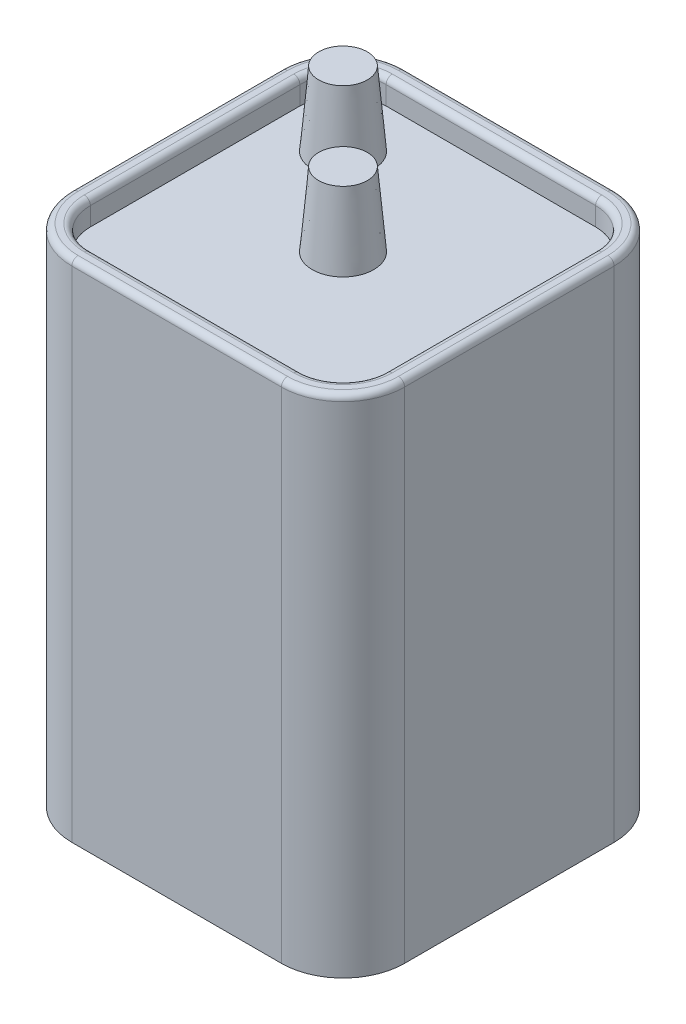
SolidWorks part; units mm, degrees
ref_plane "Front Plane" through (0, 0, 0) normal (0, 0, 1) x (1, 0, 0)
ref_plane "Top Plane" through (0, 0, 0) normal (0, 1, 0) x (1, 0, 0)
ref_plane "Right Plane" through (0, 0, 0) normal (1, 0, 0) x (0, 0, -1)
sketch "Sketch2" plane through (0, 0, 0) normal (0, 1, 0) x (1, 0, 0)
  line L1 (-34.29, 34.29) -> (34.29, 34.29)
  line L2 (-34.29, 34.29) -> (-34.29, -34.29)
  line L3 (-34.29, -34.29) -> (34.29, -34.29)
  line L4 (34.29, 34.29) -> (34.29, -34.29)
  line L5 (0, -34.29) -> (0, 34.29) construction
  line L6 (-34.29, 0) -> (34.29, 0) construction
  point P1 (0, 0)
  dimension "D1" = 68.58
  dimension "D2" = 68.58
extrude "Base-Extrude" add sketch "Sketch2" along normal blind 104.14
fillet "Side Fillets" radius 12.7 4 edges at (-34.29, 52.07, 34.29) (-34.29, 52.07, -34.29) (34.29, 52.07, -34.29) (34.29, 52.07, 34.29)
sketch "Sketch5" plane through (0, 104.14, 0) normal (0, 1, 0) x (1, 0, 0)
  line L8 (-30.48, 21.59) -> (-30.48, -21.59)
  line L10 (-30.48, 21.59) -> (-30.48, -21.59)
  line L16 (-21.59, -30.48) -> (21.59, -30.48)
  line L18 (-21.59, -30.48) -> (21.59, -30.48)
  line L20 (30.48, -21.59) -> (30.48, 21.59)
  line L21 (30.48, -21.59) -> (30.48, 21.59)
  line L22 (21.59, 30.48) -> (-21.59, 30.48)
  line L23 (21.59, 30.48) -> (-21.59, 30.48)
  arc A8 (-30.48, -21.59) -> (-21.59, -30.48) centre (-21.59, -21.59) ccw
  arc A9 (-30.48, -21.59) -> (-21.59, -30.48) centre (-21.59, -21.59) ccw
  arc A10 (21.59, -30.48) -> (30.48, -21.59) centre (21.59, -21.59) ccw
  arc A11 (21.59, -30.48) -> (30.48, -21.59) centre (21.59, -21.59) ccw
  arc A16 (30.48, 21.59) -> (21.59, 30.48) centre (21.59, 21.59) ccw
  arc A17 (30.48, 21.59) -> (21.59, 30.48) centre (21.59, 21.59) ccw
  arc A18 (-21.59, 30.48) -> (-30.48, 21.59) centre (-21.59, 21.59) ccw
  arc A19 (-21.59, 30.48) -> (-30.48, 21.59) centre (-21.59, 21.59) ccw
  dimension "D1" = 3.81
extrude "Top Cut" cut sketch "Sketch5" against normal blind 5.08
fillet "Top Face Fillet" radius 1.27 16 edges at (-30.5703, 104.14, -30.5703) (0, 104.14, -34.29) (30.5703, 104.14, -30.5703) (34.29, 104.14, 0) (30.5703, 104.14, 30.5703) (0, 104.14, 34.29) (-30.5703, 104.14, 30.5703) (-34.29, 104.14, 0) (-30.48, 104.14, 0) (-27.8762, 104.14, 27.8762) (0, 104.14, 30.48) (27.8762, 104.14, 27.8762) (30.48, 104.14, 0) (27.8762, 104.14, -27.8762) (0, 104.14, -30.48) (-27.8762, 104.14, -27.8762)
sketch "Sketch9" plane through (0, 99.06, 0) normal (0, 1, 0) x (1, 0, 0)
  line L0 (-17.9605, 17.9605) -> (0, 0) construction
  line L1 (0, -37.719) -> (0, 37.719) construction
  circle A0 centre (0, 0) radius 6.35
  circle A1 centre (-17.9605, 17.9605) radius 6.35
  dimension "D1" = 12.7
  dimension "D2" = 25.4
  dimension "D3" = 45
extrude "Terminals" add sketch "Sketch9" along normal blind 15.24 draft 5
